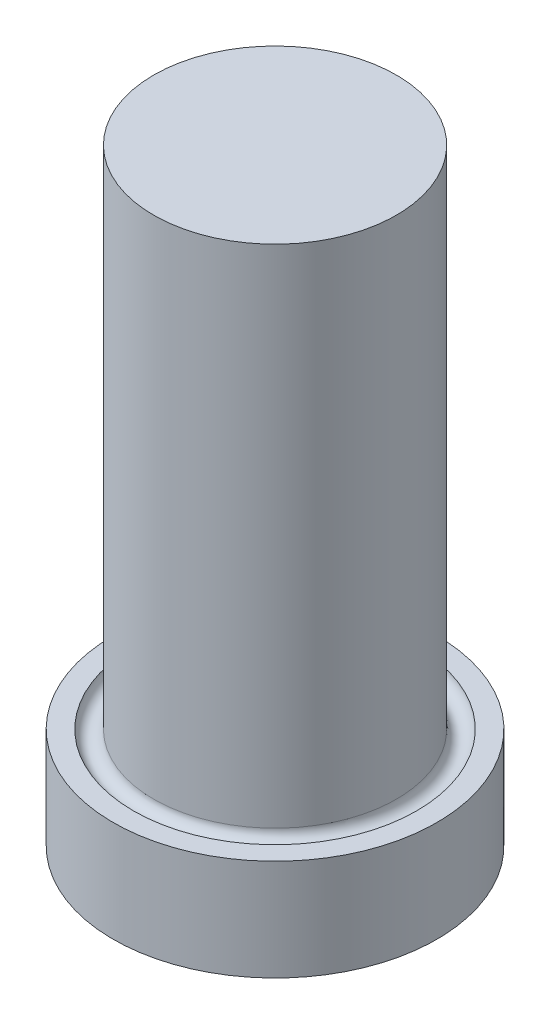
SolidWorks part; units mm, degrees
material "AISI 304"
ref_plane "Front Plane" through (0, 0, 0) normal (0, 0, 1) x (1, 0, 0)
ref_plane "Top Plane" through (0, 0, 0) normal (0, 1, 0) x (1, 0, 0)
ref_plane "Right Plane" through (0, 0, 0) normal (1, 0, 0) x (0, 0, -1)
sketch "Sketch1" plane through (0, 0, 0) normal (0, 0, 1) x (1, 0, 0)
  line L1 (0, 0) -> (6, 0)
  line L2 (0, 0) -> (0, -25)
  line L4 (6, 0) -> (6, -25)
  line L5 (7, -25) -> (8, -25)
  line L6 (0, -25) -> (0, -30)
  line L7 (0, -30) -> (8, -30)
  line L8 (8, -25) -> (8, -30)
  arc A0 (6, -25) -> (7, -25) centre (6.5, -25) ccw
  dimension "D5" = 1
  dimension "D1" = 6
  dimension "D2" = 25
  dimension "D3" = 8
  dimension "D4" = 5
  dimension "D6" = 0
  dimension "D7" = 0
revolve "Revolve1" add sketch "Sketch1" angle 360 about L2
